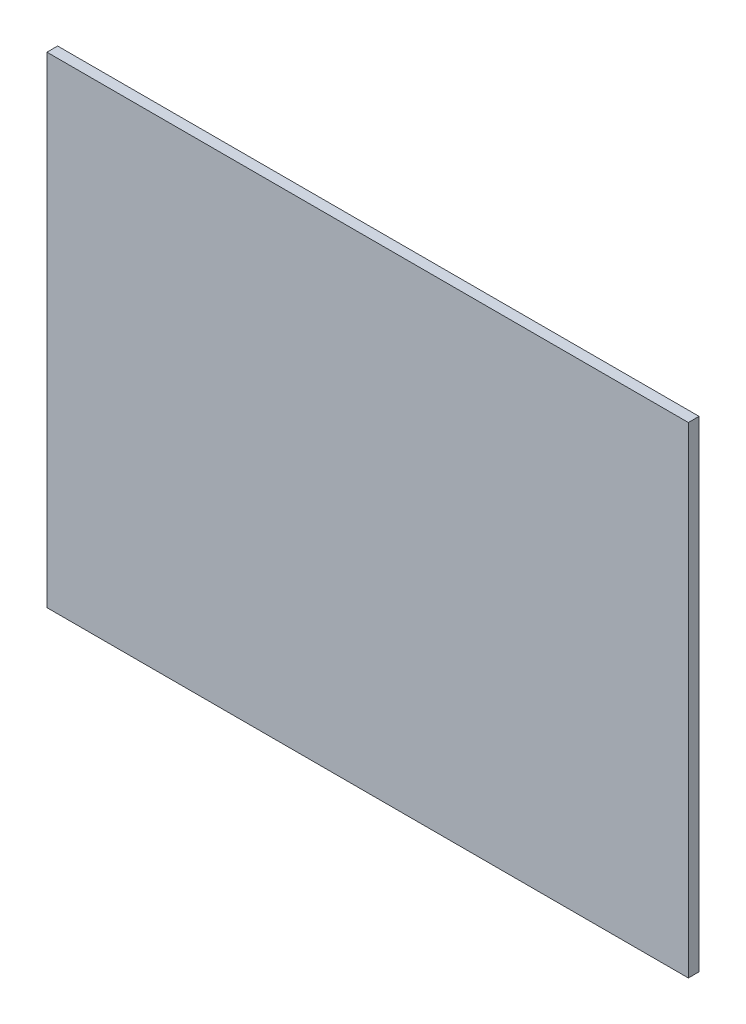
SolidWorks part; units mm, degrees
ref_plane "Alzado" through (0, 0, 0) normal (0, 0, 1) x (1, 0, 0)
ref_plane "Planta" through (0, 0, 0) normal (0, 1, 0) x (1, 0, 0)
ref_plane "Vista lateral" through (0, 0, 0) normal (1, 0, 0) x (0, 0, -1)
sketch "Croquis1" plane through (0, 0, 0) normal (0, 0, 1) x (1, 0, 0)
  line L0 (-61.8018, 42.9699) -> (538.1982, 42.9699)
  line L1 (538.1982, 42.9699) -> (538.1982, -407.0301)
  line L2 (538.1982, -407.0301) -> (-61.8018, -407.0301)
  line L3 (-61.8018, -407.0301) -> (-61.8018, 42.9699)
  dimension "D1" = 600
  dimension "D2" = 450
extrude "Saliente-Extruir1" add sketch "Croquis1" along normal blind 10
